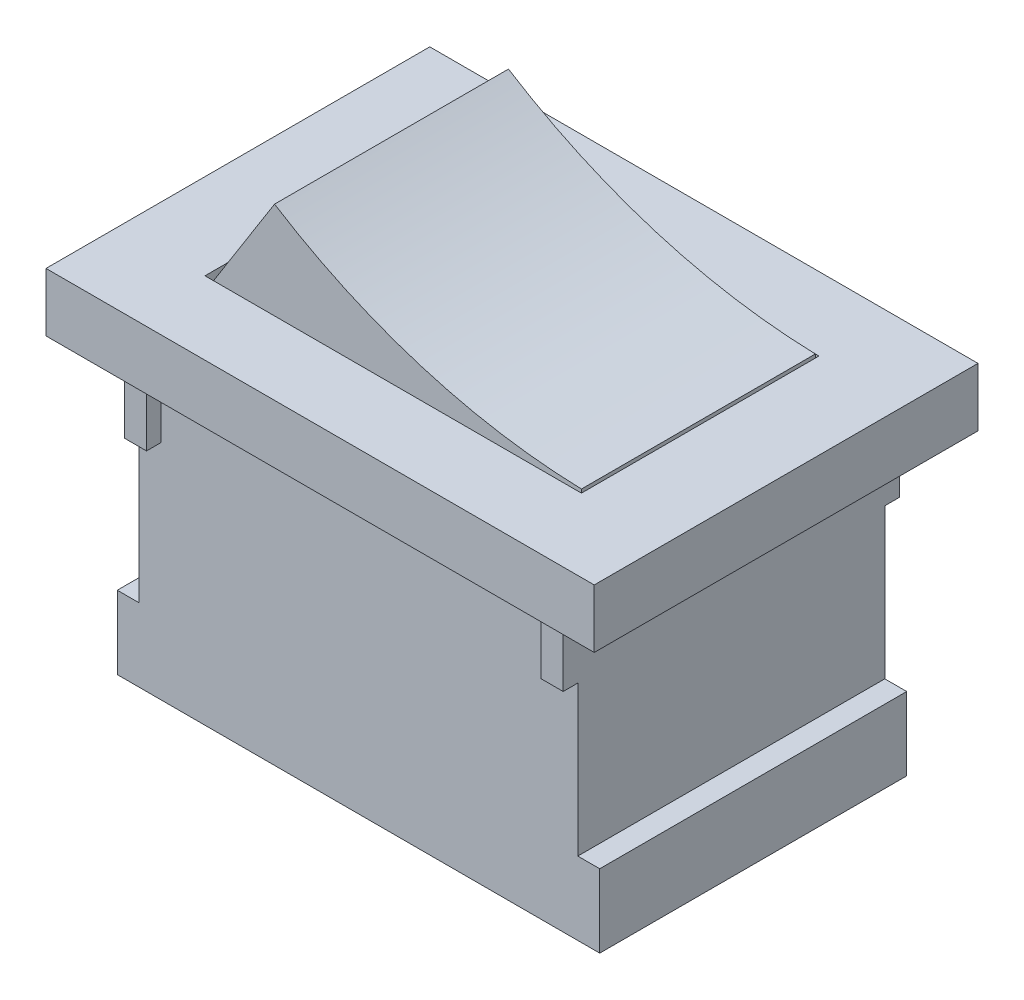
SolidWorks part; units mm, degrees
ref_plane "Front Plane" through (0, 0, 0) normal (0, 0, 1) x (1, 0, 0)
ref_plane "Top Plane" through (0, 0, 0) normal (0, 1, 0) x (1, 0, 0)
ref_plane "Right Plane" through (0, 0, 0) normal (1, 0, 0) x (0, 0, -1)
sketch "Sketch1" plane through (0, 0, 0) normal (0, 1, 0) x (1, 0, 0)
  line L1 (-7.5, -5.25) -> (7.5, -5.25)
  line L2 (-7.5, -5.25) -> (-7.5, 5.25)
  line L3 (-7.5, 5.25) -> (7.5, 5.25)
  line L4 (7.5, -5.25) -> (7.5, 5.25)
  line L5 (-7.5, -5.25) -> (7.5, 5.25) construction
  line L6 (-7.5, 5.25) -> (7.5, -5.25) construction
  point P0 (0, 0)
  dimension "D1" = 15
  dimension "D2" = 10.5
extrude "Boss-Extrude1" add sketch "Sketch1" along normal blind 1.6
sketch "Sketch2" plane through (0, 1.6, 0) normal (0, 1, 0) x (1, 0, 0)
  line L1 (-5.15, 3.25) -> (5.15, 3.25)
  line L2 (-5.15, 3.25) -> (-5.15, -3.25)
  line L3 (-5.15, -3.25) -> (5.15, -3.25)
  line L4 (5.15, 3.25) -> (5.15, -3.25)
  line L5 (-5.15, 3.25) -> (5.15, -3.25) construction
  line L6 (-5.15, -3.25) -> (5.15, 3.25) construction
  point P0 (0, 0)
  dimension "D1" = 10.3
  dimension "D2" = 6.5
extrude "Cut-Extrude1" cut sketch "Sketch2" against normal blind 1.5
sketch "Sketch3" plane through (0, 0.1, 0) normal (0, 1, 0) x (1, 0, 0)
  line L1 (-5.1, -3.2) -> (5.1, -3.2)
  line L2 (-5.1, -3.2) -> (-5.1, 3.2)
  line L3 (-5.1, 3.2) -> (5.1, 3.2)
  line L4 (5.1, -3.2) -> (5.1, 3.2)
  line L5 (-5.1, -3.2) -> (5.1, 3.2) construction
  line L6 (-5.1, 3.2) -> (5.1, -3.2) construction
  point P0 (0, 0)
  dimension "D1" = 10.2
  dimension "D2" = 6.4
extrude "Boss-Extrude2" add sketch "Sketch3" along normal blind 4.1
sketch "Sketch4" plane through (0, 0, 3.2) normal (0, 0, 1) x (1, 0, 0)
  line L0 (-5.1, 1.3383) -> (-3.2966, 4.2)
  line L1 (-5.1, 4.2) -> (5.1, 4.2) construction
  line L2 (5.1, 4.2) -> (5.1, 0.1) construction
  line L7 (-5.1, 0.1) -> (5.1, 0.1)
  line L8 (5.1, 0.1) -> (5.1, 4.2)
  line L9 (5.1, 4.2) -> (-5.1, 4.2)
  line L10 (-5.1, 4.2) -> (-5.1, 0.1)
  line L11 (-5.1, 0.1) -> (5.1, 0.1)
  line L12 (5.1, 0.1) -> (5.1, 4.2)
  line L13 (5.1, 4.2) -> (-5.1, 4.2)
  line L14 (-5.1, 4.2) -> (-5.1, 0.1)
  arc A0 (-3.2966, 4.2) -> (5.1, 1.648) centre (5.5618, 18.2566) ccw
  point P10 (-5.2217, 1.047)
  point P12 (-5.1, 1.3836)
  point P14 (0, 0)
  point P15 (0, 0)
  point P16 (-5.1, 1.3571)
  point P17 (5.1, 1.7111)
  point P18 (-5.1, 1.3383)
  line M8 (5.1, 4.2) -> (-5.1, 4.2)
  line M9 (-5.1, 4.2) -> (-5.1, 0.1)
  dimension "D1" = 0
extrude "Cut-Extrude4" cut sketch "Sketch4" against normal blind 6.4 contours L0 M9 M8 | A0 L12 M8
sketch "Sketch8" plane through (0, 0, 0) normal (0, -1, 0) x (-1, 0, 0)
  line L1 (-6.6, 4.2) -> (6.6, 4.2)
  line L2 (-6.6, 4.2) -> (-6.6, -4.2)
  line L3 (-6.6, -4.2) -> (6.6, -4.2)
  line L4 (6.6, 4.2) -> (6.6, -4.2)
  line L5 (-6.6, 4.2) -> (6.6, -4.2) construction
  line L6 (-6.6, -4.2) -> (6.6, 4.2) construction
  point P0 (0, 0)
  dimension "D1" = 8.4
  dimension "D2" = 13.2
extrude "Boss-Extrude5" add sketch "Sketch8" along normal blind 8.1 separate body
sketch "Sketch9" plane through (0, 0, 4.2) normal (0, 0, 1) x (1, 0, 0)
  line L0 (-6.6, 0) -> (-6, 0)
  line L1 (6.6, 0) -> (-6.6, 0) construction
  line L2 (-6, 0) -> (-6, -6.1)
  line L3 (-6, -6.1) -> (-6.6, -6.1)
  line L4 (-6.6, -8.1) -> (-6.6, 0) construction
  line L5 (-6.6, -6.1) -> (-6.6, 0)
  line L6 (-7.5, 1.6) -> (-7.5, 0) construction
  line L7 (6.6, -8.1) -> (-6.6, -8.1) construction
  line L8 (0, 0) -> (0, -8.1) construction
  line L9 (-7.5, 0) -> (7.5, 0) construction
  line L10 (6, -6.1) -> (6.6, -6.1)
  line L11 (6, 0) -> (6, -6.1)
  line L12 (6.6, 0) -> (6, 0)
  line L13 (6.6, -6.1) -> (6.6, 0)
  point P11 (-6.3, -6.1)
  dimension "D1" = 1.5
  dimension "D2" = 2
extrude "Cut-Extrude30" cut sketch "Sketch9" against normal blind 8.4
sketch "Sketch10" plane through (0, 0, -4.2) normal (0, 0, -1) x (-1, 0, 0)
  line L0 (-6, 0) -> (-5.4, 0)
  line L1 (6, 0) -> (-6, 0) construction
  line L2 (-5.4, 0) -> (-5.4, -2)
  line L3 (-5.4, -2) -> (-6, -2)
  line L4 (-6, 0) -> (-6, -6.1) construction
  line L5 (-6, -2) -> (-6, 0)
  line L6 (0, -0.3195) -> (0, 0)
  line L7 (5.4, -2) -> (6, -2)
  line L8 (5.4, 0) -> (5.4, -2)
  line L9 (6, 0) -> (5.4, 0)
  line L10 (6, -2) -> (6, 0)
  line L19 (6, 0) -> (-6, 0)
  line L20 (6, -6.1) -> (6, 0)
  line L21 (6.6, -6.1) -> (6, -6.1)
  line L22 (6.6, -8.1) -> (6.6, -6.1)
  line L23 (-6.6, -8.1) -> (6.6, -8.1)
  line L24 (-6.6, -6.1) -> (-6.6, -8.1)
  line L25 (-6, -6.1) -> (-6.6, -6.1)
  line L26 (-6, 0) -> (-6, -6.1)
  line L27 (6, 0) -> (-6, 0)
  line L28 (6, -6.1) -> (6, 0)
  line L29 (6.6, -6.1) -> (6, -6.1)
  line L30 (6.6, -8.1) -> (6.6, -6.1)
  line L31 (-6.6, -8.1) -> (6.6, -8.1)
  line L32 (-6.6, -6.1) -> (-6.6, -8.1)
  line L33 (-6, -6.1) -> (-6.6, -6.1)
  line L34 (-6, 0) -> (-6, -6.1)
  line M8 (6, 0) -> (-6, 0)
  line M9 (-6, 0) -> (-6, -6.1)
  dimension "D1" = 2
  dimension "D2" = 0.6
  dimension "D3" = 0
extrude "Boss-Extrude7" add sketch "Sketch10" along normal blind 0.4 contours L3 L2 M8 M9 | L9 L8 L7 L10
pattern_linear "LPattern3" count 2 spacing 8.8 along (0, 0, 1) of "Boss-Extrude7"
sketch "Sketch12" plane through (-6, 0, 0) normal (-1, 0, 0) x (0, 0, 1)
  line L1 (-0.8599, -0.0228) -> (0.8599, -0.0228)
  line L2 (-0.8599, -0.0228) -> (-0.8599, -6.0681)
  line L3 (-0.8599, -6.0681) -> (0.8599, -6.0681)
  line L4 (0.8599, -0.0228) -> (0.8599, -6.0681)
  line L5 (-0.8599, -0.0228) -> (0.8599, -6.0681) construction
  line L6 (-0.8599, -6.0681) -> (0.8599, -0.0228) construction
  point P0 (0, -3.0454)
extrude "Boss-Extrude8" add sketch "Sketch12" along normal blind 1.1
sketch "Sketch14" plane through (0, 0, -0.8599) normal (0, 0, -1) x (-1, 0, 0)
  line L0 (6, -0.0228) -> (6.59, -3.0675)
  line L1 (6.59, -3.0675) -> (6, -6.0681)
  line L2 (6.4225, -0.0228) -> (7.0127, -3.0681)
  line L3 (7.0127, -3.0681) -> (6.4228, -6.0681)
  line L4 (6.4072, 0.0561) -> (7.0127, -3.0681) construction
  line L5 (7.0127, -3.0681) -> (6.407, -6.1481) construction
  line L6 (7.1, -6.0681) -> (6, -6.0681) construction
  line L7 (6, -6.1) -> (6, -2) construction
  line L9 (7.1, -0.0228) -> (6, -0.0228) construction
  line L14 (6, -0.0228) -> (6, -6.0681)
  line L15 (7.1, -0.0228) -> (6, -0.0228)
  line L16 (7.1, -6.0681) -> (7.1, -0.0228)
  line L17 (6, -6.0681) -> (7.1, -6.0681)
  line L18 (6, -0.0228) -> (6, -6.0681)
  line L19 (7.1, -0.0228) -> (6, -0.0228)
  line L20 (7.1, -6.0681) -> (7.1, -0.0228)
  line L21 (6, -6.0681) -> (7.1, -6.0681)
  point P16 (6.4228, -0.0228)
  dimension "D1" = 0.59
  dimension "D2" = 3
  dimension "D3" = 1.0127
  dimension "D4" = 0
extrude "Cut-Extrude42" cut sketch "Sketch14" against normal blind 1.1 contours L2 L3 L1 L4 L5
